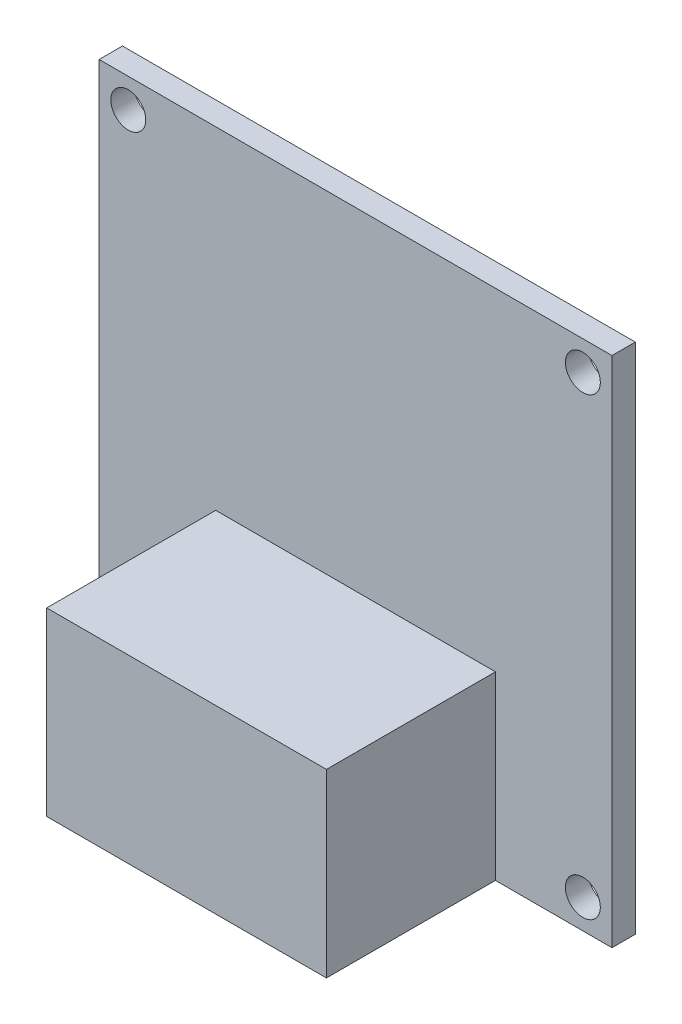
SolidWorks part; units mm, degrees
ref_plane "Alzado" through (0, 0, 0) normal (0, 0, 1) x (1, 0, 0)
ref_plane "Planta" through (0, 0, 0) normal (0, 1, 0) x (1, 0, 0)
ref_plane "Vista lateral" through (0, 0, 0) normal (1, 0, 0) x (0, 0, -1)
sketch "Croquis1" plane through (0, 0, 0) normal (0, 0, 1) x (1, 0, 0)
  line L0 (19.5, 22) -> (19.5, -22) construction
  line L1 (22, -22) -> (-22, -22)
  line L2 (22, -22) -> (22, 22)
  line L3 (22, 22) -> (-22, 22)
  line L4 (-22, -22) -> (-22, 22)
  line L5 (22, -22) -> (-22, 22) construction
  line L6 (22, 22) -> (-22, -22) construction
  line L7 (-19.5, 22) -> (-19.5, -22) construction
  line L8 (-22, 19.5) -> (22, 19.5) construction
  line L9 (-22, -19.5) -> (22, -19.5) construction
  line L10 (0, -22) -> (0, 22) construction
  circle A0 centre (19.5, 19.5) radius 1.5
  circle A1 centre (19.5, -19.5) radius 1.5
  circle A2 centre (-19.5, -19.5) radius 1.5
  circle A3 centre (-19.5, 19.5) radius 1.5
  point P0 (0, 0)
  dimension "D7" = 3
  dimension "D1" = 44
  dimension "D2" = 44
  dimension "D3" = 2.5
  dimension "D4" = 2.5
  dimension "D5" = 2.5
  dimension "D6" = 2.5
extrude "Saliente-Extruir1" add sketch "Croquis1" along normal blind 2
sketch "Croquis2" plane through (0, 0, 2) normal (0, 0, 1) x (1, 0, 0)
  line L0 (12, -22) -> (12, -6.5)
  line L1 (-22, -22) -> (22, -22) construction
  line L2 (12, -6.5) -> (-12, -6.5)
  line L3 (-12, -6.5) -> (-12, -22)
  line L4 (22, -22) -> (22, 22) construction
  line L5 (-22, 22) -> (-22, -22) construction
  line L6 (12, -22) -> (-12, -22)
  dimension "D1" = 10
  dimension "D2" = 10
  dimension "D3" = 15.5
extrude "Saliente-Extruir2" add sketch "Croquis2" along normal blind 14.5 separate body
